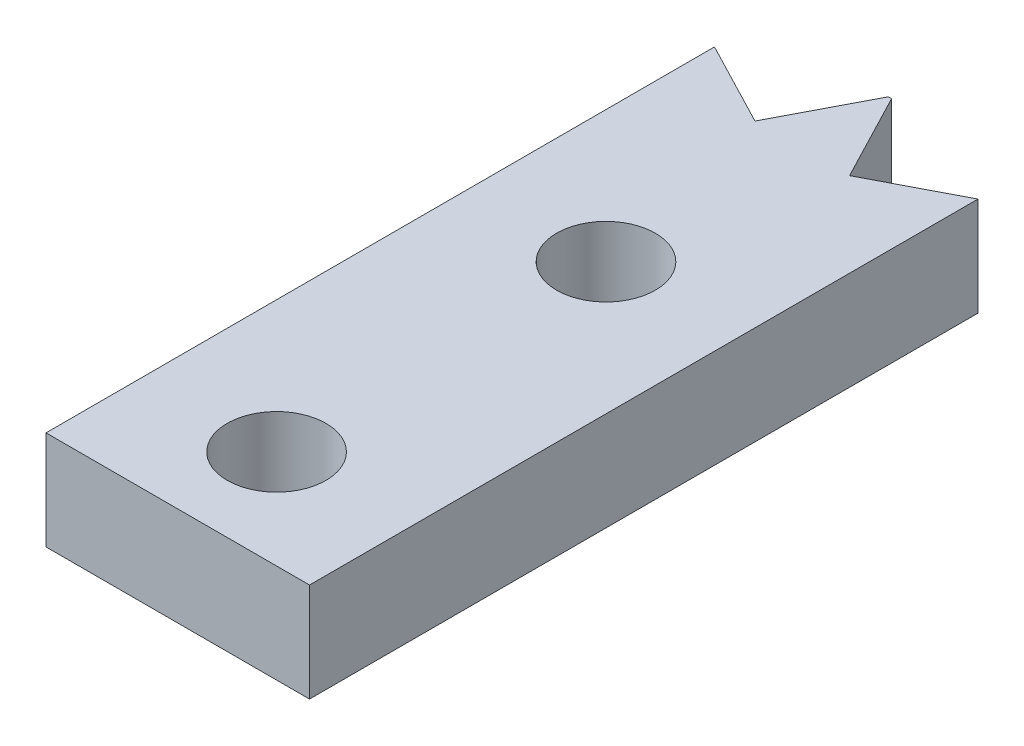
SolidWorks part; units mm, degrees
ref_plane "Front Plane" through (0, 0, 0) normal (0, 0, 1) x (1, 0, 0)
ref_plane "Top Plane" through (0, 0, 0) normal (0, 1, 0) x (1, 0, 0)
ref_plane "Right Plane" through (0, 0, 0) normal (1, 0, 0) x (0, 0, -1)
sketch "Sketch1" plane through (0, 0, 0) normal (0, 1, 0) x (1, 0, 0)
  line L29 (1.1574, 21.7244) -> (3.8185, 20.3392)
  line L30 (5.2037, 23.0002) -> (3.8185, 20.3392)
  line L31 (1.1574, 21.7244) -> (0.7537, 21.7244)
  line L32 (0.7537, 21.7244) -> (0.7537, 0)
  line L36 (5.2037, 23.0002) -> (5.3037, 23.0002)
  line L38 (0.7537, 0) -> (9.7537, 0)
  line L39 (9.7537, 21.7244) -> (9.7537, 0)
  line L40 (9.35, 21.7244) -> (9.7537, 21.7244)
  line L41 (5.3037, 23.0002) -> (6.689, 20.3392)
  line L42 (9.35, 21.7244) -> (6.689, 20.3392)
  line L43 (5.2537, 23.0002) -> (5.2537, 0)
  dimension "D1" = 3
  dimension "D2" = 3
  dimension "D3" = 152.5
  dimension "D4" = 270
  dimension "D5" = 3
  dimension "D6" = 3
  dimension "D7" = 90
  dimension "D8" = 152.5
  dimension "D9" = 270
  dimension "D10" = 0.1
  dimension "D11" = 0.4037
  dimension "D12" = 9
  dimension "D13" = 0.4037
extrude "Boss-Extrude3" add sketch "Sketch1" along normal blind 3 contours L36 L43 L38 L39 L40 L42 L41 | L43 L36 L30 L29 L31 L32 L38
sketch "Sketch3" plane through (0, 3, 0) normal (0, 1, 0) x (1, 0, 0)
  line L0 (5.2537, 0) -> (5.2537, 23.0002)
  line L1 (0.7537, 0) -> (9.7537, 0) construction
  point P4 (5.2537, 4.38)
  point P7 (5.2537, 14.38)
  dimension "D1" = 4.38
  dimension "D2" = 10
hole_wizard "M3 Clearance Hole1" positions "3DSketch1" profile "Sketch4" hole size "M3" standard "ANSI Metric"
sketch3d "3DSketch1"
  point P0 (5.2537, 3, -14.38)
  point P3 (5.2537, 3, -4.38)
sketch "Sketch4" plane through (5.2537, 3, -14.38) normal (1, 0, 0) x (0, 0, 1)
  line L0 (0, 0) -> (0, 10.9013)
  line L1 (0, 10.9013) -> (1.5, 10)
  line L2 (1.5, 10) -> (1.5, 0)
  line L5 (1.5, 0) -> (0, 0)
  line L10 (0, 10.9013) -> (-1.5, 10) construction
  line L11 (0, -6.35) -> (0, 107.95) construction
  dimension "Hole Dia." = 3
  dimension "Hole Depth" = 10
  dimension "Drill Angle" = 118
sketch "Sketch5" plane through (0, 0, 0) normal (0, -1, 0) x (-1, 0, 0)
  line L1 (-0.7537, 0) -> (-1.2537, 0)
  line L2 (-0.7537, 0) -> (-0.7537, 21.7244)
  line L3 (-0.7537, 21.7244) -> (-1.2537, 21.7244)
  line L4 (-1.2537, 0) -> (-1.2537, 21.7244)
  line L5 (-9.7537, 0) -> (-9.2537, 0)
  line L6 (-9.7537, 0) -> (-9.7537, 21.7244)
  line L7 (-9.7537, 21.7244) -> (-9.2537, 21.7244)
  line L8 (-9.2537, 0) -> (-9.2537, 21.7244)
  line L9 (-1.1574, 21.7244) -> (-0.7537, 21.7244) construction
  line L10 (-9.35, 21.7244) -> (-9.7537, 21.7244) construction
  point P14 (-9.5519, 21.7244)
  dimension "D1" = 0.5
  dimension "D2" = 0
  dimension "D3" = 0
  dimension "D4" = 0.5
extrude "Cut-Extrude1" cut sketch "Sketch5" against normal blind 10
sketch "Sketch6" plane through (0, 0, 0) normal (0, 0, 1) x (1, 0, 0)
  line L0 (9.2537, 3) -> (9.2537, 0) construction
  line L1 (1.2537, 3) -> (9.2537, 3)
  line L2 (1.2537, 3) -> (1.2537, 0)
  line L3 (1.2537, 0) -> (9.2537, 0)
  line L4 (9.2537, 3) -> (9.2537, 0)
extrude "Cut-Extrude2" cut sketch "Sketch6" against normal blind 1.38
